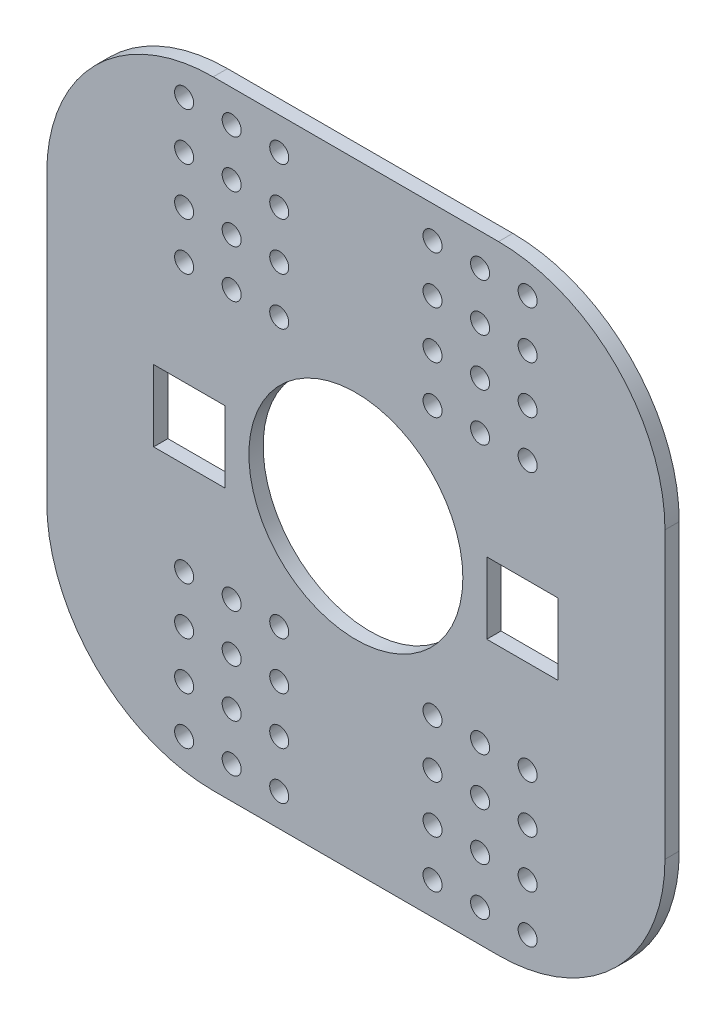
SolidWorks part; units mm, degrees
ref_plane "前视基准面" through (0, 0, 0) normal (0, 0, 1) x (1, 0, 0)
ref_plane "上视基准面" through (0, 0, 0) normal (0, 1, 0) x (1, 0, 0)
ref_plane "右视基准面" through (0, 0, 0) normal (1, 0, 0) x (0, 0, -1)
sketch "草图1" plane through (0, 0, 0) normal (0, 0, 1) x (1, 0, 0)
  line L1 (-65, 65) -> (65, 65)
  line L2 (-65, 65) -> (-65, -65)
  line L3 (-65, -65) -> (65, -65)
  line L4 (65, 65) -> (65, -65)
  line L5 (-65, 65) -> (65, -65) construction
  line L6 (-65, -65) -> (65, 65) construction
  circle A0 centre (0, 0) radius 22.5
  point P0 (0, 0)
extrude "凸台-拉伸1" add sketch "草图1" against normal blind 3
fillet "圆角1" radius 35 4 edges at (65, 65, -1.5) (-65, 65, -1.5) (65, -65, -1.5) (-65, -65, -1.5)
sketch "草图5" plane through (0, 0, -3) normal (0, 0, -1) x (-1, 0, 0)
  line L4 (42.532, -8.6552) -> (42.532, 6.3448)
  line L5 (42.532, 6.3448) -> (27.532, 6.3448)
  line L6 (27.532, 6.3448) -> (27.532, -8.6552)
  line L7 (27.532, -8.6552) -> (42.532, -8.6552)
  line L8 (42.532, -8.6552) -> (42.532, 6.3448)
  line L9 (42.532, 6.3448) -> (27.532, 6.3448)
  line L10 (27.532, 6.3448) -> (27.532, -8.6552)
  line L11 (27.532, -8.6552) -> (42.532, -8.6552)
  line L12 (-27.532, 6.3448) -> (-42.532, 6.3448)
  line L13 (-42.532, 6.3448) -> (-42.532, -8.6552)
  line L14 (-42.532, -8.6552) -> (-27.532, -8.6552)
  line L15 (-27.532, -8.6552) -> (-27.532, 6.3448)
  line L16 (-27.532, 6.3448) -> (-42.532, 6.3448)
  line L17 (-42.532, 6.3448) -> (-42.532, -8.6552)
  line L18 (-42.532, -8.6552) -> (-27.532, -8.6552)
  line L19 (-27.532, -8.6552) -> (-27.532, 6.3448)
  circle A1 centre (36.1191, 58.1968) radius 2
  circle A2 centre (36.1191, 58.1968) radius 2
  circle A3 centre (36.1191, 48.1968) radius 2
  circle A4 centre (36.1191, 48.1968) radius 2
  circle A5 centre (36.1191, 38.1968) radius 2
  circle A6 centre (36.1191, 38.1968) radius 2
  circle A7 centre (-36.1191, -58.1968) radius 2
  circle A8 centre (-36.1191, -58.1968) radius 2
  circle A9 centre (16.1191, 48.1968) radius 2
  circle A10 centre (16.1191, 48.1968) radius 2
  circle A11 centre (16.1191, 38.1968) radius 2
  circle A12 centre (16.1191, 38.1968) radius 2
  circle A13 centre (16.1191, 28.1968) radius 2
  circle A14 centre (16.1191, 28.1968) radius 2
  circle A15 centre (26.1191, 58.1968) radius 2
  circle A16 centre (26.1191, 58.1968) radius 2
  circle A17 centre (16.1191, -48.1968) radius 2
  circle A18 centre (16.1191, -48.1968) radius 2
  circle A19 centre (26.1191, -28.1968) radius 2
  circle A20 centre (26.1191, -28.1968) radius 2
  circle A21 centre (36.1191, 28.1968) radius 2
  circle A22 centre (36.1191, 28.1968) radius 2
  circle A23 centre (26.1191, 48.1968) radius 2
  circle A24 centre (26.1191, 48.1968) radius 2
  circle A25 centre (26.1191, 38.1968) radius 2
  circle A26 centre (26.1191, 38.1968) radius 2
  circle A27 centre (26.1191, 28.1968) radius 2
  circle A28 centre (26.1191, 28.1968) radius 2
  circle A29 centre (16.1191, 58.1968) radius 2
  circle A30 centre (16.1191, 58.1968) radius 2
  circle A31 centre (16.1191, -58.1968) radius 2
  circle A32 centre (16.1191, -58.1968) radius 2
  circle A33 centre (26.1191, -58.1968) radius 2
  circle A34 centre (26.1191, -58.1968) radius 2
  circle A35 centre (16.1191, -28.1968) radius 2
  circle A36 centre (16.1191, -28.1968) radius 2
  circle A37 centre (16.1191, -38.1968) radius 2
  circle A38 centre (16.1191, -38.1968) radius 2
  circle A39 centre (36.1191, -38.1968) radius 2
  circle A40 centre (36.1191, -38.1968) radius 2
  circle A41 centre (36.1191, -48.1968) radius 2
  circle A42 centre (36.1191, -48.1968) radius 2
  circle A43 centre (36.1191, -58.1968) radius 2
  circle A44 centre (36.1191, -58.1968) radius 2
  circle A45 centre (-36.1191, -48.1968) radius 2
  circle A46 centre (-36.1191, -48.1968) radius 2
  circle A47 centre (-36.1191, -38.1968) radius 2
  circle A48 centre (-36.1191, -38.1968) radius 2
  circle A49 centre (-16.1191, -38.1968) radius 2
  circle A50 centre (-16.1191, -38.1968) radius 2
  circle A51 centre (-16.1191, -28.1968) radius 2
  circle A52 centre (-16.1191, -28.1968) radius 2
  circle A53 centre (-26.1191, -58.1968) radius 2
  circle A54 centre (-26.1191, -58.1968) radius 2
  circle A55 centre (26.1191, -38.1968) radius 2
  circle A56 centre (26.1191, -38.1968) radius 2
  circle A57 centre (26.1191, -48.1968) radius 2
  circle A58 centre (26.1191, -48.1968) radius 2
  circle A59 centre (36.1191, -28.1968) radius 2
  circle A60 centre (36.1191, -28.1968) radius 2
  circle A61 centre (-36.1191, -28.1968) radius 2
  circle A62 centre (-36.1191, -28.1968) radius 2
  circle A63 centre (-26.1191, -48.1968) radius 2
  circle A64 centre (-26.1191, -48.1968) radius 2
  circle A65 centre (-26.1191, -38.1968) radius 2
  circle A66 centre (-26.1191, -38.1968) radius 2
  circle A67 centre (-26.1191, -28.1968) radius 2
  circle A68 centre (-26.1191, -28.1968) radius 2
  circle A69 centre (-16.1191, -48.1968) radius 2
  circle A70 centre (-16.1191, -48.1968) radius 2
  circle A71 centre (-16.1191, 28.1968) radius 2
  circle A72 centre (-16.1191, 28.1968) radius 2
  circle A73 centre (-16.1191, 38.1968) radius 2
  circle A74 centre (-16.1191, 38.1968) radius 2
  circle A75 centre (-16.1191, 48.1968) radius 2
  circle A76 centre (-16.1191, 48.1968) radius 2
  circle A77 centre (-26.1191, 28.1968) radius 2
  circle A78 centre (-26.1191, 28.1968) radius 2
  circle A79 centre (-26.1191, 38.1968) radius 2
  circle A80 centre (-26.1191, 38.1968) radius 2
  circle A81 centre (-36.1191, 38.1968) radius 2
  circle A82 centre (-36.1191, 38.1968) radius 2
  circle A83 centre (-36.1191, 48.1968) radius 2
  circle A84 centre (-36.1191, 48.1968) radius 2
  circle A85 centre (-36.1191, 58.1968) radius 2
  circle A86 centre (-36.1191, 58.1968) radius 2
  circle A87 centre (-16.1191, -58.1968) radius 2
  circle A88 centre (-16.1191, -58.1968) radius 2
  circle A89 centre (-16.1191, 58.1968) radius 2
  circle A90 centre (-16.1191, 58.1968) radius 2
  circle A91 centre (-26.1191, 58.1968) radius 2
  circle A92 centre (-26.1191, 58.1968) radius 2
  circle A93 centre (-26.1191, 48.1968) radius 2
  circle A94 centre (-26.1191, 48.1968) radius 2
  circle A95 centre (-36.1191, 28.1968) radius 2
  circle A96 centre (-36.1191, 28.1968) radius 2
  dimension "D1" = 0
  dimension "D2" = 0
  dimension "D3" = 0
  dimension "D4" = 0
  dimension "D5" = 0
  dimension "D6" = 0
  dimension "D7" = 0
  dimension "D8" = 0
  dimension "D9" = 0
  dimension "D10" = 0
  dimension "D11" = 0
  dimension "D12" = 0
  dimension "D13" = 0
  dimension "D14" = 0
  dimension "D15" = 0
  dimension "D16" = 0
  dimension "D17" = 0
  dimension "D18" = 0
  dimension "D19" = 0
  dimension "D20" = 0
  dimension "D21" = 0
  dimension "D22" = 0
  dimension "D23" = 0
  dimension "D24" = 0
  dimension "D25" = 0
  dimension "D26" = 0
  dimension "D27" = 0
  dimension "D28" = 0
  dimension "D29" = 0
  dimension "D30" = 0
  dimension "D31" = 0
  dimension "D32" = 0
  dimension "D33" = 0
  dimension "D34" = 0
  dimension "D35" = 0
  dimension "D36" = 0
  dimension "D37" = 0
  dimension "D38" = 0
  dimension "D39" = 0
  dimension "D40" = 0
  dimension "D41" = 0
  dimension "D42" = 0
  dimension "D43" = 0
  dimension "D44" = 0
  dimension "D45" = 0
  dimension "D46" = 0
  dimension "D47" = 0
  dimension "D48" = 0
  dimension "D49" = 0
  dimension "D50" = 0
extrude "切除-拉伸2" cut sketch "草图5" against normal blind 13
